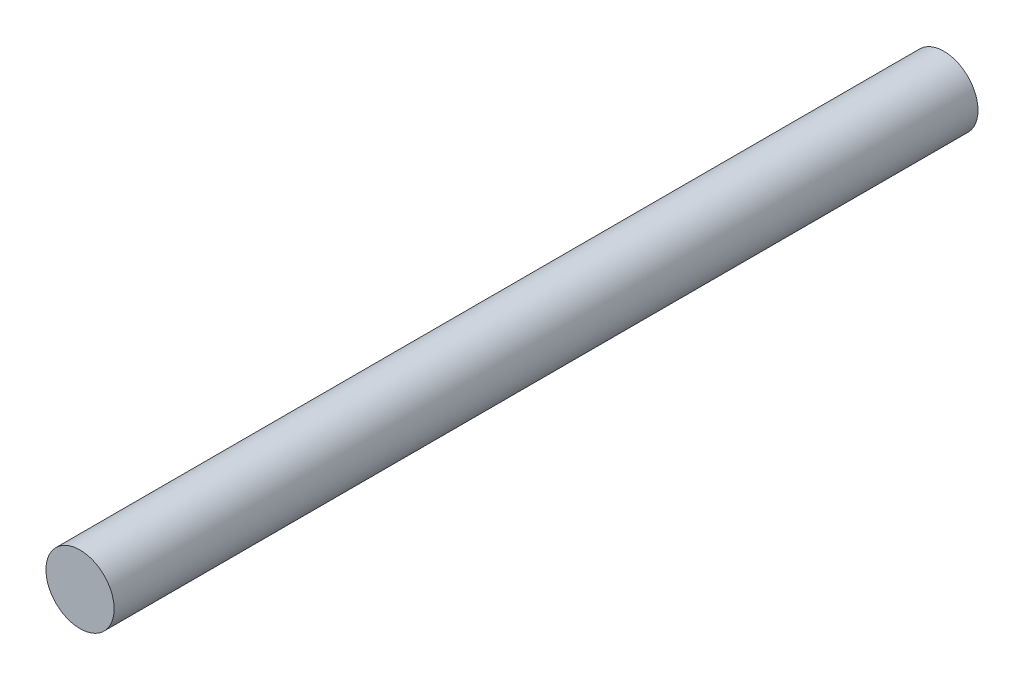
SolidWorks part; units mm, degrees
ref_plane "Ön Düzlem" through (0, 0, 0) normal (0, 0, 1) x (1, 0, 0)
ref_plane "Üst Düzlem" through (0, 0, 0) normal (0, 1, 0) x (1, 0, 0)
ref_plane "Sağ Düzlem" through (0, 0, 0) normal (1, 0, 0) x (0, 0, -1)
sketch "Sketch1" plane through (0, 0, 0) normal (0, 0, 1) x (1, 0, 0)
  circle A0 centre (0, 0) radius 1.5
  dimension "D1" = 3
extrude "Boss-Extrude1" add sketch "Sketch1" along normal blind 38
